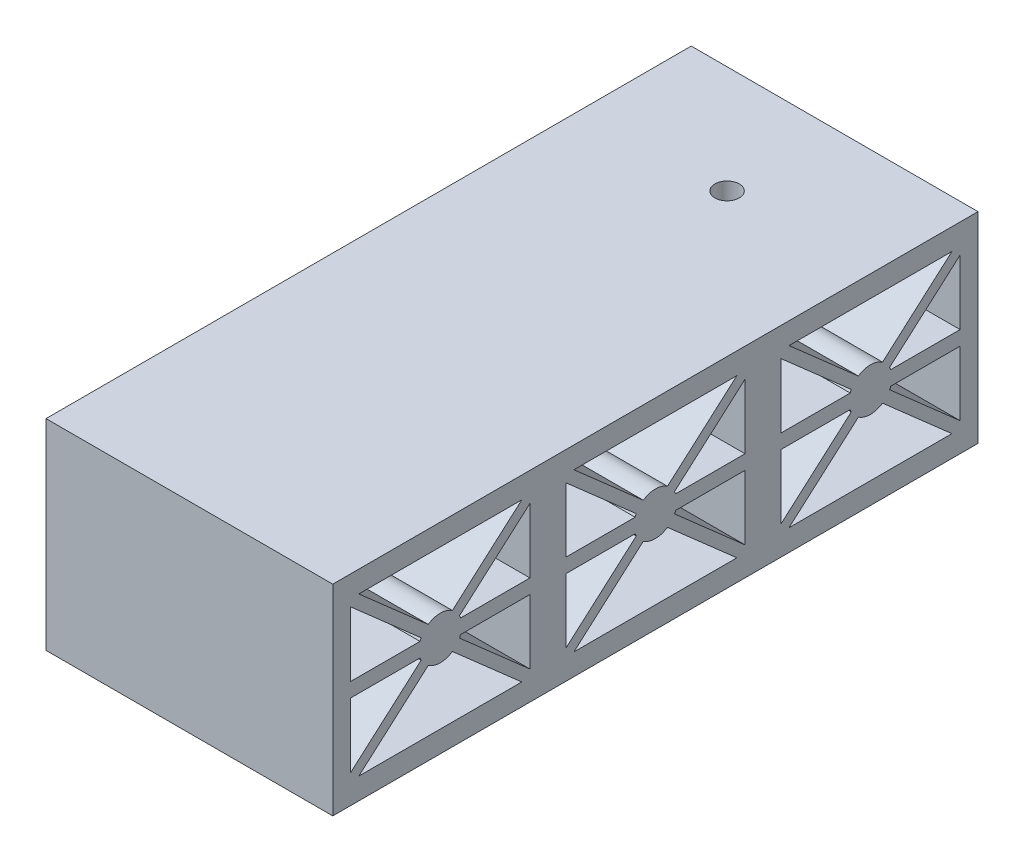
SolidWorks part; units mm, degrees
ref_plane "Front Plane" through (0, 0, 0) normal (0, 0, 1) x (1, 0, 0)
ref_plane "Top Plane" through (0, 0, 0) normal (0, 1, 0) x (1, 0, 0)
ref_plane "Right Plane" through (0, 0, 0) normal (1, 0, 0) x (0, 0, -1)
sketch "Sketch19" plane through (0, 0, 0) normal (1, 0, 0) x (0, 0, -1)
  line L1 (16, 4) -> (-14, 4)
  line L2 (16, 4) -> (16, -24)
  line L3 (16, -24) -> (-14, -24)
  line L4 (-14, 4) -> (-14, -24)
  line L9 (1, 1) -> (1, -21) construction
  line L10 (-11.5, -10) -> (13.5, -10) construction
  line L11 (13.5, -21) -> (-11.5, -21)
  line L12 (13.5, -21) -> (13.5, 1)
  line L13 (13.5, 1) -> (-11.5, 1)
  line L14 (-11.5, -21) -> (-11.5, 1)
  line L15 (1, 1) -> (1, -21) construction
  line L16 (13.5, -10) -> (-11.5, -10) construction
  point P4 (1, -10)
  point P6 (1, -10)
  point P10 (-14, -10)
  dimension "D1" = 30
  dimension "D2" = 3
  dimension "D3" = 3
  dimension "D4" = 2.5
  dimension "D5" = 2.5
extrude "Boss-Extrude1" add sketch "Sketch19" against normal blind 40
sketch "Sketch21" plane through (0, 0, 0) normal (1, 0, 0) x (0, 0, -1)
  line L0 (1, -10) -> (3.1213, -7.8787) construction
  line L1 (1, -10) -> (-1.1213, -7.8787) construction
  line L2 (1, -10) -> (-1.1213, -12.1213) construction
  line L3 (1, -10) -> (1.7932, -12.8932) construction
  line L4 (-2, -10) -> (4, -10) construction
  line L5 (-11.5, 1) -> (-11.5, -21) construction
  line L6 (-11.5, -9) -> (13.5, -9)
  line L7 (-11.5, -9) -> (-11.5, -11)
  line L8 (-11.5, -11) -> (13.5, -11)
  line L9 (13.5, -9) -> (13.5, -11)
  line L10 (1, -11) -> (1, -9) construction
  line L11 (-11.5, -10) -> (13.5, -10) construction
  line L12 (-11.9955, -20.437) -> (13.0045, 1.563)
  line L13 (-11.9955, -20.437) -> (-11.0045, -21.563)
  line L14 (13.0045, 1.563) -> (13.9955, 0.437)
  line L15 (-11.0045, -21.563) -> (13.9955, 0.437)
  line L16 (13.5, 1) -> (-11.5, -21) construction
  line L17 (0.5045, -9.437) -> (1.4955, -10.563) construction
  line L18 (13.9955, -20.437) -> (-11.0045, 1.563)
  line L19 (13.9955, -20.437) -> (13.0045, -21.563)
  line L20 (-11.0045, 1.563) -> (-11.9955, 0.437)
  line L21 (13.0045, -21.563) -> (-11.9955, 0.437)
  line L22 (-11.5, 1) -> (13.5, -21) construction
  line L23 (1.4955, -9.437) -> (0.5045, -10.563) construction
  circle A0 centre (1, -10) radius 3
  dimension "D1" = 6
  dimension "D2" = 2
  dimension "D3" = 1.5
  dimension "D4" = 1.5
extrude "Boss-Extrude2" add sketch "Sketch21" against normal up to surface (40 mm away) contours A0 L18 L20 L21 | A0 L15 L14 L12 | A0 L6 L7 L8 | A0 L8 L9 L6 | A0 L12 L13 L15 | A0 L21 L19 L18 | L15 A0 L21 | L12 A0 L15 L21 L8 | L8 L21 L12 | L6 A0 L8 L12 L21 | L21 L12 L6 | L18 A0 L21 L6 L12 | L12 A0 L18 | L15 A0 L12 L18 L6 | L18 L15 L6 | L8 A0 L6 L15 L18 | L8 L18 L15 | L21 A0 L18 L8 L15 | L21 L8 L15 L18 L6 L12 up to face at (-40, -10, -1)
sketch "Sketch22" plane through (0, 4, 0) normal (0, 1, 0) x (1, 0, 0)
  line L0 (-20, -14) -> (-40, -14) construction
  line L1 (-40, -14) -> (0, -14) construction
  line L2 (-20, -14) -> (0, -14) construction
  circle A2 centre (-20, 1) radius 1.7
  dimension "D1" = 3.4
sketch "Sketch32" plane through (0, -24, 0) normal (0, -1, 0) x (-1, 0, 0)
  line L0 (40, 16) -> (0, 16) construction
  line L7 (16.5359, 1) -> (18.2679, -2)
  line L8 (18.2679, -2) -> (21.7321, -2)
  line L9 (21.7321, -2) -> (23.4641, 1)
  line L10 (23.4641, 1) -> (21.7321, 4)
  line L11 (21.7321, 4) -> (18.2679, 4)
  line L12 (18.2679, 4) -> (16.5359, 1)
  circle A1 centre (20, 1) radius 3 construction
  dimension "D1" = 6
pattern_linear "LPattern2" count 3 spacing 30 along (0, 0, 1) of bodies 139
extrude "Cut-Extrude1" cut sketch "Sketch22" against normal through all
extrude "Cut-Extrude2" cut sketch "Sketch32" against normal blind 2.32
combine bodies "Combine1" operation type add bodies to combine 151 148 149
